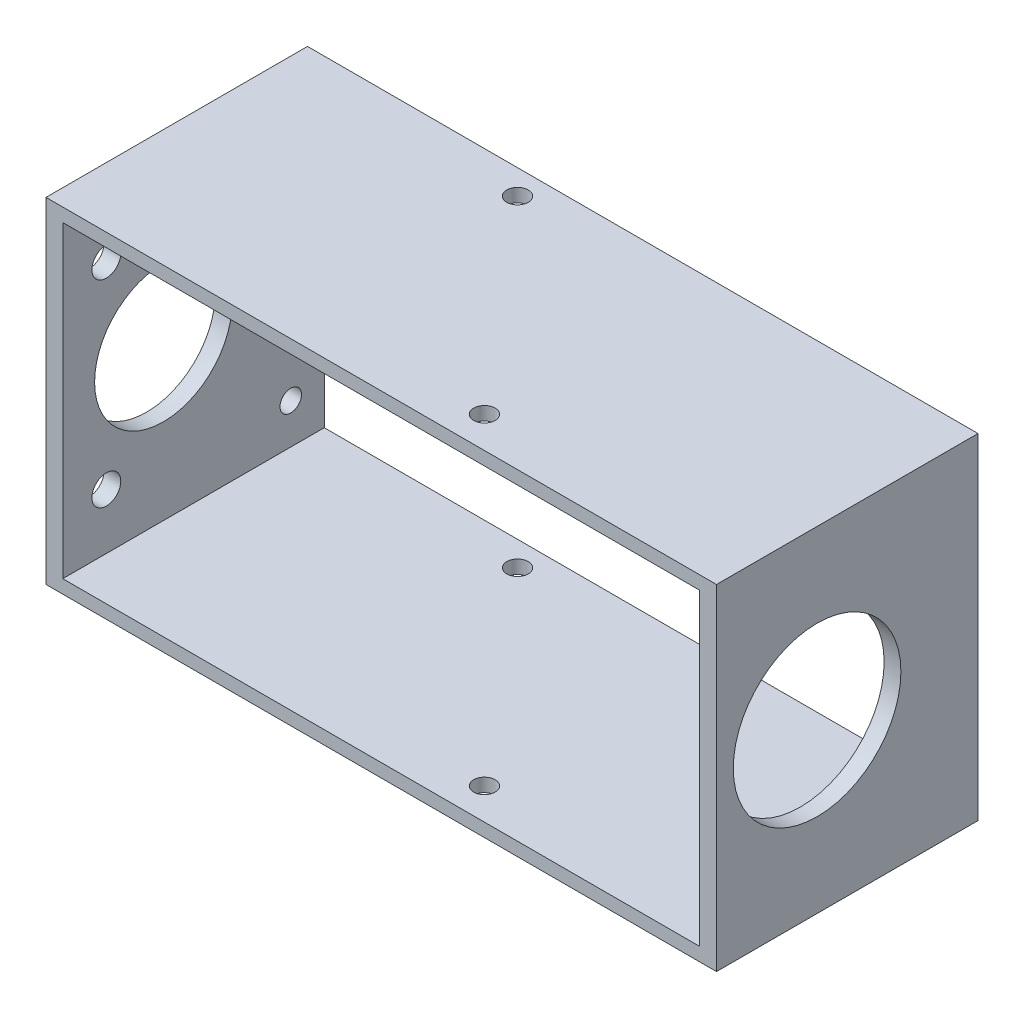
SolidWorks part; units mm, degrees
ref_plane "正面" through (0, 0, 0) normal (0, 0, 1) x (1, 0, 0)
ref_plane "平面" through (0, 0, 0) normal (0, 1, 0) x (1, 0, 0)
ref_plane "右側面" through (0, 0, 0) normal (1, 0, 0) x (0, 0, -1)
sketch "ｽｹｯﾁ1" plane through (0, 0, 0) normal (0, 0, 1) x (1, 0, 0)
  line L1 (-50, -25) -> (50, -25)
  line L2 (-50, -25) -> (-50, 25)
  line L3 (-50, 25) -> (50, 25)
  line L4 (50, -25) -> (50, 25)
  line L5 (-50, -25) -> (50, 25) construction
  line L6 (-50, 25) -> (50, -25) construction
  line L7 (-47.5, -23) -> (47.5, -23)
  line L8 (-47.5, -23) -> (-47.5, 23)
  line L9 (-47.5, 23) -> (47.5, 23)
  line L10 (47.5, -23) -> (47.5, 23)
  line L11 (-47.5, -23) -> (47.5, 23) construction
  line L12 (-47.5, 23) -> (47.5, -23) construction
  point P0 (0, 0)
  point P6 (0, 0)
  dimension "D1" = 2
  dimension "D2" = 2.5
  dimension "D3" = 50
  dimension "D4" = 100
extrude "ﾎﾞｽ - 押し出し1" add sketch "ｽｹｯﾁ1" along normal mid plane 39
sketch "ｽｹｯﾁ2" plane through (0, 25, 0) normal (0, 1, 0) x (1, 0, 0)
  line L0 (-15, 15.8209) -> (10.7115, -14.8209) construction
  line L1 (-2.1442, 0.5) -> (50, 0.5) construction
  line L2 (50, -19.5) -> (50, 19.5) construction
  line L3 (50, -19.5) -> (-50, -19.5) construction
  circle A0 centre (-15, 15.8209) radius 1.6
  circle A1 centre (10.7115, -14.8209) radius 1.6
  point P10 (2.8558, 0.5)
  point P11 (-10, 15.8209)
  dimension "D2" = 3.2
  dimension "D5" = 65
  dimension "D1" = 40
  dimension "D3" = 20
  dimension "D4" = 50
extrude "ｶｯﾄ - 押し出し1" cut sketch "ｽｹｯﾁ2" against normal through all
sketch "ｽｹｯﾁ3" plane through (-50, 0, 0) normal (-1, 0, 0) x (0, 0, 1)
  line L0 (4.5, 0) -> (4.5, 21.5) construction
  line L1 (19.5, 25) -> (19.5, -25) construction
  line L2 (-30.7, -9) -> (-30.7, 9) construction
  line L3 (21.45, 0) -> (-21.45, 0) construction
  line L4 (-12.5, 0) -> (4.5, 0) construction
  line L5 (-14.5, -17) -> (-14.5, 17) construction
  line L6 (19.5, 25) -> (-19.5, 25) construction
  line L7 (-19.5, 25) -> (-19.5, -25) construction
  circle A0 centre (4.5, 0) radius 21.5 construction
  circle A1 centre (4.5, 0) radius 10.25
  circle A3 centre (-30.7, 0) radius 6.05 construction
  circle A4 centre (-30.7, -9) radius 1.6 construction
  circle A5 centre (-30.7, 9) radius 1.6 construction
  circle A8 centre (-12.5, 0) radius 2.15
  circle A9 centre (4.5, 0) radius 17 construction
  circle A10 centre (13, 14.7224) radius 2.15
  circle A11 centre (13, -14.7224) radius 2.15
  circle A12 centre (-14.5, -17) radius 1.6
  circle A13 centre (-14.5, 17) radius 1.6
  point P12 (-30.7, 0)
  point P18 (-14.5, 0)
  point P21 (4.5, 0)
  point P28 (4.5, 0)
  dimension "D1" = 43
  dimension "D3" = 20.5
  dimension "D6" = 3.2
  dimension "D8" = 12.1
  dimension "D4" = 4.3
  dimension "D10" = 34
  dimension "D2" = 3.2
  dimension "D5" = 15
  dimension "D7" = 18
  dimension "D9" = 35.2
  dimension "D12" = 8
  dimension "D13" = 5
  dimension "D11" = 3
extrude "ｶｯﾄ - 押し出し2" cut sketch "ｽｹｯﾁ3" against normal up to next
sketch "ｽｹｯﾁ4" plane through (50, 0, 0) normal (1, 0, 0) x (0, 0, -1)
  circle A0 centre (-4.5, 0) radius 12.5
  circle A1 centre (-4.5, 0) radius 10.25 construction
  dimension "D1" = 25
extrude "ｶｯﾄ - 押し出し3" cut sketch "ｽｹｯﾁ4" against normal up to next
equation "\"D9@ｽｹｯﾁ3\"=(66+22)*0.8/2"
